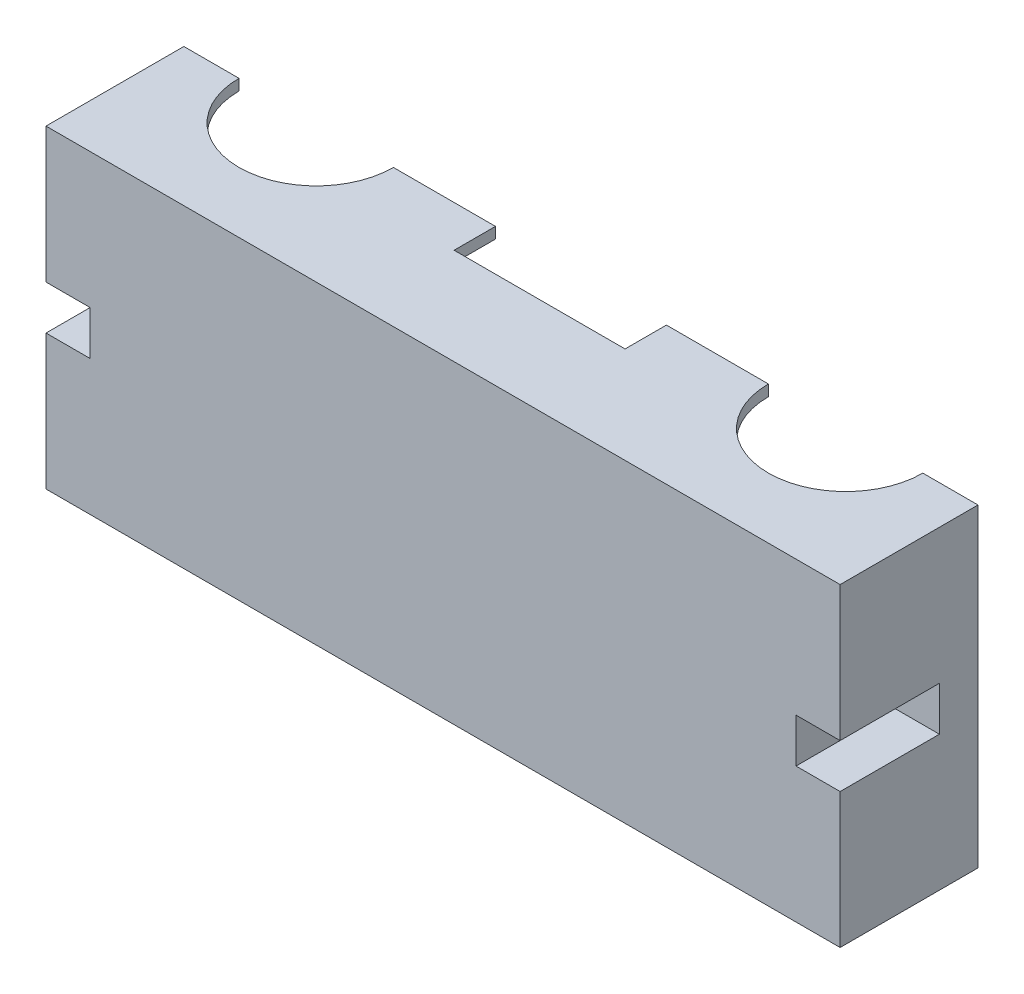
SolidWorks part; units mm, degrees
ref_plane "Ebene vorne" through (0, 0, 0) normal (0, 0, 1) x (1, 0, 0)
ref_plane "Ebene oben" through (0, 0, 0) normal (0, 1, 0) x (1, 0, 0)
ref_plane "Ebene rechts" through (0, 0, 0) normal (1, 0, 0) x (0, 0, -1)
sketch "Skizze1" plane through (0, 0, 0) normal (0, 0, 1) x (1, 0, 0)
  line L1 (-102.9591, -27.5852) -> (41.0409, -27.5852)
  line L2 (-102.9591, -27.5852) -> (-102.9591, 29.4148)
  line L3 (-102.9591, 29.4148) -> (41.0409, 29.4148)
  line L4 (41.0409, -27.5852) -> (41.0409, 29.4148)
  dimension "D1" = 144
  dimension "D2" = 57
extrude "Aufsatz-Linear austragen1" add sketch "Skizze1" along normal blind 25
sketch "Skizze2" plane through (0, 0, 25) normal (0, 0, 1) x (1, 0, 0)
  line L0 (41.0409, -27.5852) -> (41.0409, 29.4148) construction
  line L1 (41.0409, 4.9148) -> (33.0409, 4.9148)
  line L2 (41.0409, 4.9148) -> (41.0409, -3.0852)
  line L3 (41.0409, -3.0852) -> (33.0409, -3.0852)
  line L4 (33.0409, 4.9148) -> (33.0409, -3.0852)
  line L5 (41.0409, 29.4148) -> (-102.9591, 29.4148) construction
  line L7 (-102.9591, -27.5852) -> (41.0409, -27.5852) construction
  line L8 (-94.9591, 4.9148) -> (-102.9591, 4.9148)
  line L9 (-94.9591, 4.9148) -> (-94.9591, -3.0852)
  line L10 (-94.9591, -3.0852) -> (-102.9591, -3.0852)
  line L11 (-102.9591, 4.9148) -> (-102.9591, -3.0852)
  line L12 (-102.9591, 29.4148) -> (-102.9591, -27.5852) construction
  dimension "D1" = 8
  dimension "D2" = 8
  dimension "D3" = 24.5
  dimension "D4" = 24.5
  dimension "D5" = 0
  dimension "D6" = 24.5
  dimension "D7" = 24.5
  dimension "D8" = 8
  dimension "D9" = 8
extrude "Schnitt-Linear austragen4" cut sketch "Skizze2" against normal blind 18
sketch "Skizze5" plane through (0, 0, 0) normal (0, 0, -1) x (-1, 0, 0)
  line L0 (-41.0409, 29.4148) -> (102.9591, 29.4148) construction
  line L1 (-39.0409, 27.4148) -> (100.9591, 27.4148)
  line L2 (-39.0409, 27.4148) -> (-39.0409, 7.4148)
  line L3 (-39.0409, 7.4148) -> (100.9591, 7.4148)
  line L4 (100.9591, 27.4148) -> (100.9591, 7.4148)
  line L5 (-41.0409, -27.5852) -> (-41.0409, 29.4148) construction
  line L6 (102.9591, 29.4148) -> (102.9591, -27.5852) construction
  line L7 (-39.0409, -5.5852) -> (100.9591, -5.5852)
  line L8 (-39.0409, -5.5852) -> (-39.0409, -25.5852)
  line L9 (-39.0409, -25.5852) -> (100.9591, -25.5852)
  line L10 (100.9591, -5.5852) -> (100.9591, -25.5852)
  line L11 (102.9591, -27.5852) -> (-41.0409, -27.5852) construction
  line L13 (-31.5409, 7.4148) -> (93.4591, 7.4148)
  line L14 (-31.5409, 7.4148) -> (-31.5409, -5.5852)
  line L15 (-31.5409, -5.5852) -> (93.4591, -5.5852)
  line L16 (93.4591, 7.4148) -> (93.4591, -5.5852)
  dimension "D1" = 2
  dimension "D2" = 2
  dimension "D3" = 2
  dimension "D4" = 20
  dimension "D5" = 2
  dimension "D6" = 2
  dimension "D7" = 2
  dimension "D8" = 20
  dimension "D9" = 13
  dimension "D10" = 9.5
  dimension "D11" = 9.5
extrude "Schnitt-Linear austragen5" cut sketch "Skizze5" against normal blind 23 contours L4 L1 L2 L3 | L16 L3 L14 L7 | L10 L7 L8 L9
sketch "Skizze6" plane through (0, 29.4148, 0) normal (0, 1, 0) x (1, 0, 0)
  line L0 (41.0409, 0) -> (-102.9591, 0) construction
  line L1 (41.0409, -25) -> (41.0409, 0) construction
  line L2 (-102.9591, -25) -> (-102.9591, 0) construction
  line L4 (-15.4591, 0) -> (-46.4591, 0)
  line L5 (-15.4591, 0) -> (-15.4591, -7.5)
  line L6 (-15.4591, -7.5) -> (-46.4591, -7.5)
  line L7 (-46.4591, 0) -> (-46.4591, -7.5)
  circle A0 centre (17.0409, 0) radius 14
  circle A1 centre (-78.9591, 0) radius 14
  dimension "D1" = 24
  dimension "D2" = 0
  dimension "D3" = 24
  dimension "D4" = 31
  dimension "D5" = 7.5
  dimension "D6" = 32.5
  dimension "D7" = 32.5
extrude "Schnitt-Linear austragen6" cut sketch "Skizze6" against normal blind 2
